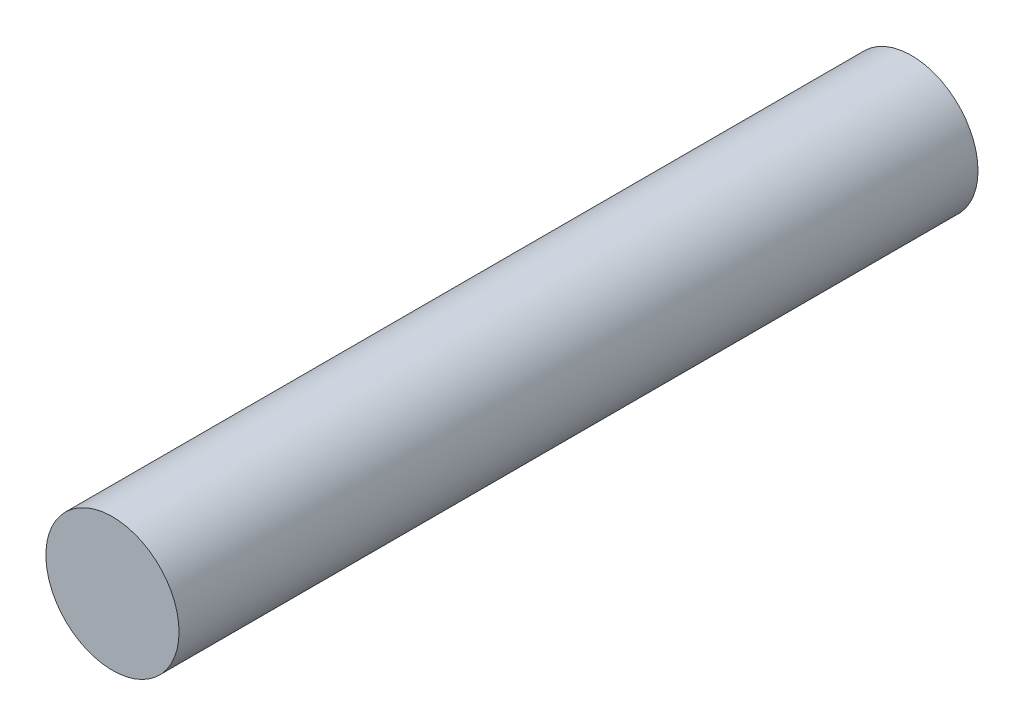
SolidWorks part; units mm, degrees
material "Acrylic (Medium-high impact)"
ref_plane "Front Plane" through (0, 0, 0) normal (0, 0, 1) x (1, 0, 0)
ref_plane "Top Plane" through (0, 0, 0) normal (0, 1, 0) x (1, 0, 0)
ref_plane "Right Plane" through (0, 0, 0) normal (1, 0, 0) x (0, 0, -1)
sketch "Sketch1" plane through (0, 0, 0) normal (0, 0, 1) x (1, 0, 0)
  circle A0 centre (0, 0) radius 1.5
  dimension "D1" = 3
extrude "Boss-Extrude1" add sketch "Sketch1" along normal blind 18
